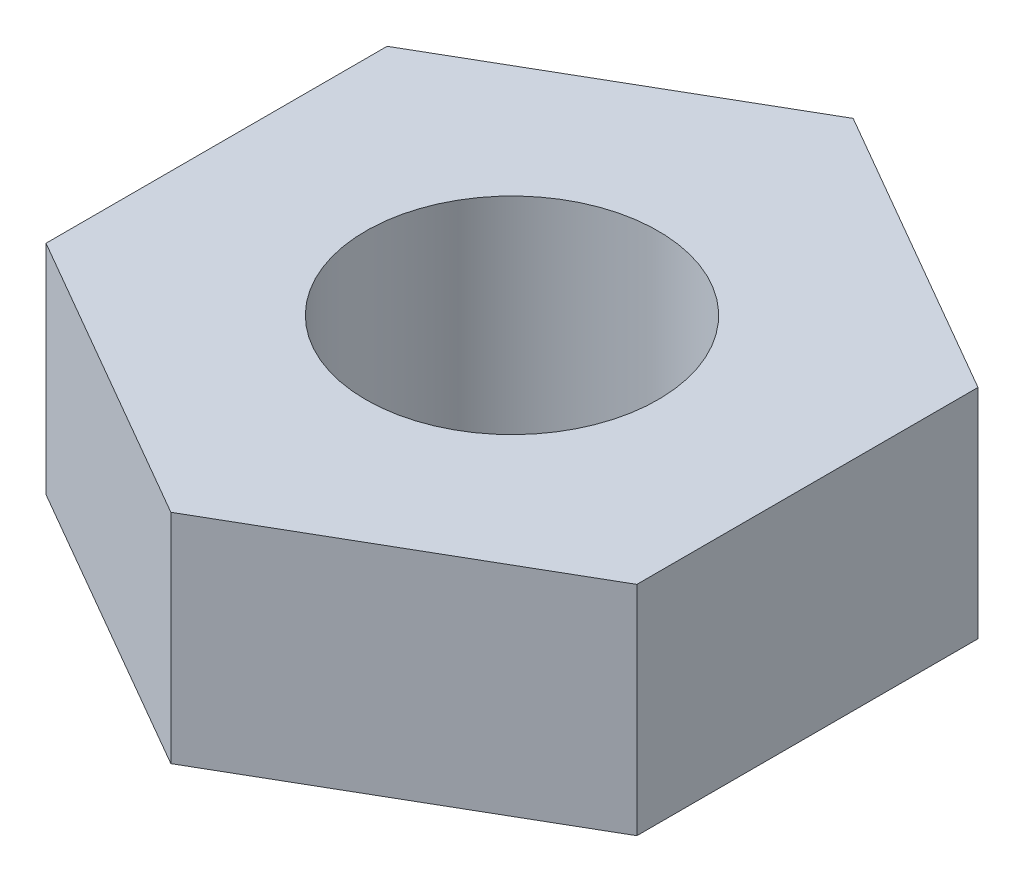
SolidWorks part; units mm, degrees
ref_plane "Alzado" through (0, 0, 0) normal (0, 0, 1) x (1, 0, 0)
ref_plane "Planta" through (0, 0, 0) normal (0, 1, 0) x (1, 0, 0)
ref_plane "Vista lateral" through (0, 0, 0) normal (1, 0, 0) x (0, 0, -1)
sketch "Croquis1" plane through (0, 0, 0) normal (0, 1, 0) x (1, 0, 0)
  line L1 (0, 5.4848) -> (-4.75, 2.7424)
  line L2 (-4.75, 2.7424) -> (-4.75, -2.7424)
  line L3 (-4.75, -2.7424) -> (0, -5.4848)
  line L4 (0, -5.4848) -> (4.75, -2.7424)
  line L5 (4.75, -2.7424) -> (4.75, 2.7424)
  line L6 (4.75, 2.7424) -> (0, 5.4848)
  circle A0 centre (0, 0) radius 2.35
  circle A1 centre (0, 0) radius 4.75 construction
  dimension "D1" = 4.7
  dimension "D2" = 9.5
extrude "Saliente-Extruir1" add sketch "Croquis1" along normal blind 3.5
